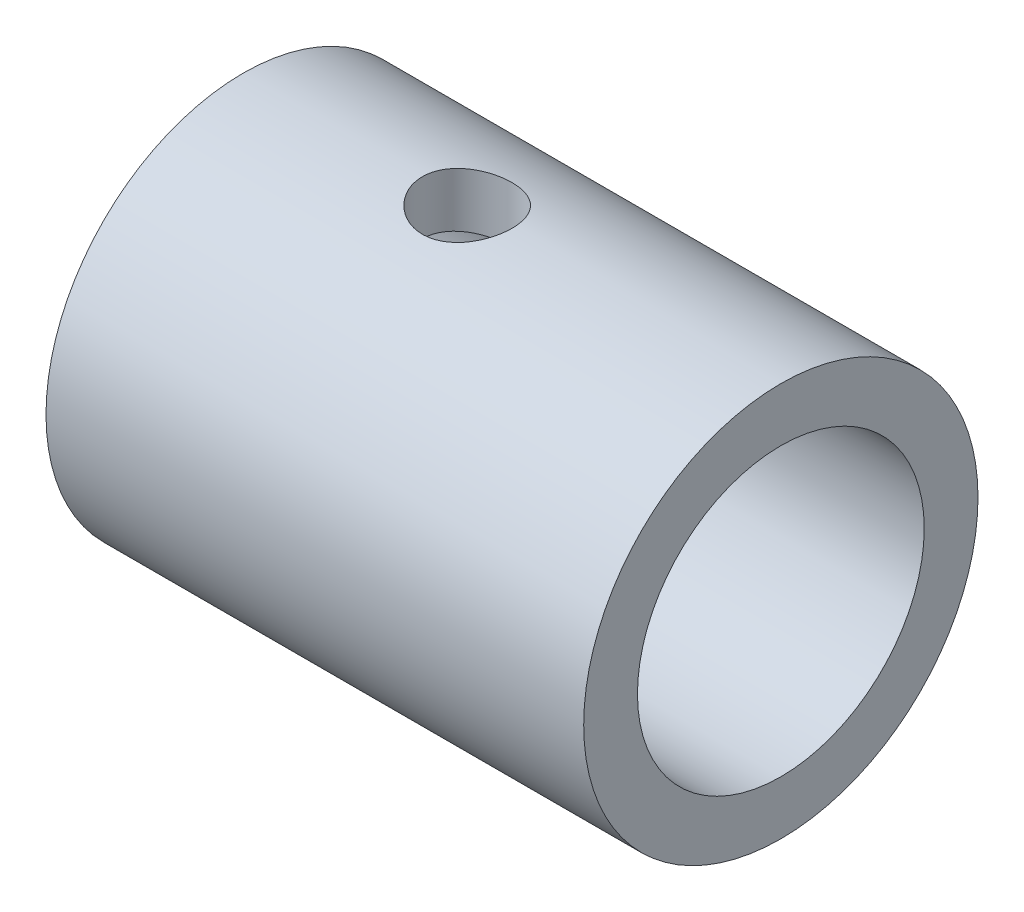
SolidWorks part; units mm, degrees
material "黄铜"
ref_plane "前视基准面" through (0, 0, 0) normal (0, 0, 1) x (1, 0, 0)
ref_plane "上视基准面" through (0, 0, 0) normal (0, 1, 0) x (1, 0, 0)
ref_plane "右视基准面" through (0, 0, 0) normal (1, 0, 0) x (0, 0, -1)
sketch "草图1" plane through (0, 0, 0) normal (1, 0, 0) x (0, 0, -1)
  circle A0 centre (0, 0) radius 8
  circle A1 centre (0, 0) radius 11
  dimension "D1" = 16
  dimension "D2" = 22
extrude "凸台-拉伸1" add sketch "草图1" against normal blind 30
sketch "草图2" plane through (0, 0, 0) normal (0, 1, 0) x (1, 0, 0)
  line L0 (-30, 0) -> (0, 0) construction
  line L1 (-30, 11) -> (-30, -11) construction
  circle A0 centre (-17.5, 0) radius 2.5
  dimension "D1" = 5
  dimension "D2" = 12.5
extrude "切除-拉伸1" cut sketch "草图2" along normal through all
